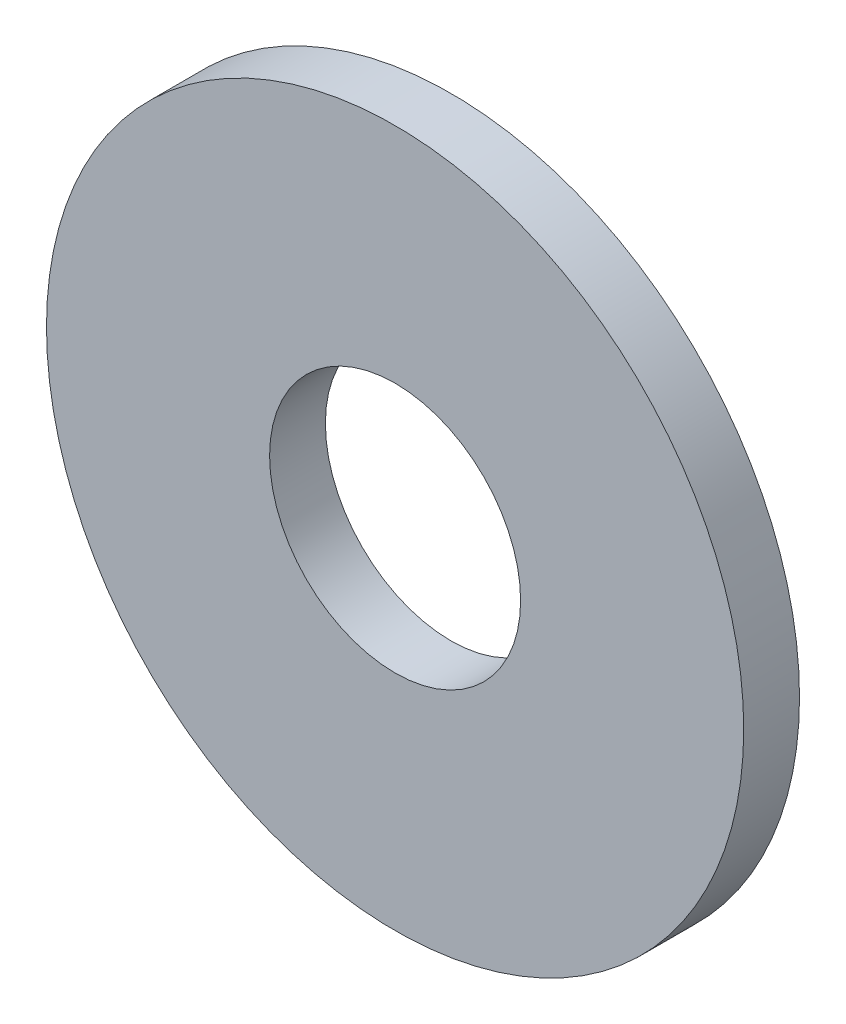
SolidWorks part; units mm, degrees
ref_plane "Front Plane" through (0, 0, 0) normal (0, 0, 1) x (1, 0, 0)
ref_plane "Top Plane" through (0, 0, 0) normal (0, 1, 0) x (1, 0, 0)
ref_plane "Right Plane" through (0, 0, 0) normal (1, 0, 0) x (0, 0, -1)
sketch "Sketch1" plane through (0, 0, 0) normal (0, 0, 1) x (1, 0, 0)
  circle A0 centre (0, 0) radius 1.8
  circle A1 centre (0, 0) radius 5
  dimension "D1" = 3.6
  dimension "D2" = 10
extrude "Boss-Extrude1" add sketch "Sketch1" along normal blind 0.8
